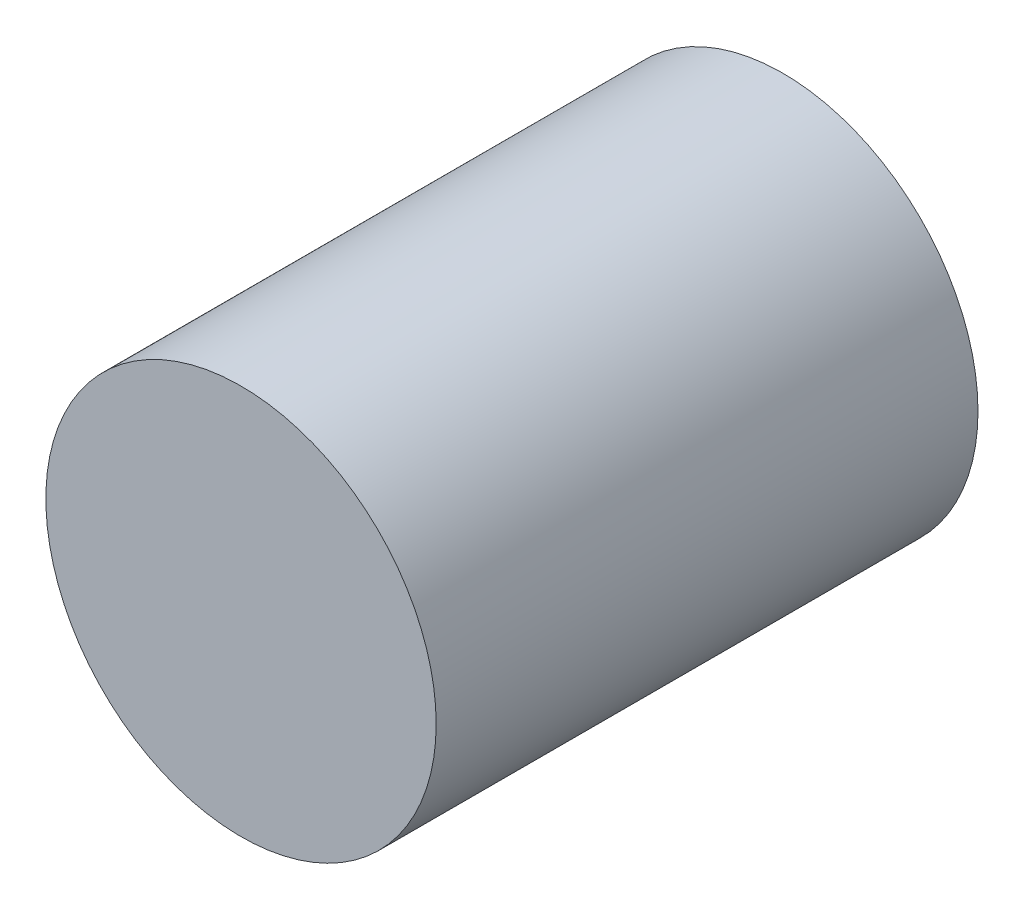
SolidWorks part; units mm, degrees
ref_plane "前视基准面" through (0, 0, 0) normal (0, 0, 1) x (1, 0, 0)
ref_plane "上视基准面" through (0, 0, 0) normal (0, 1, 0) x (1, 0, 0)
ref_plane "右视基准面" through (0, 0, 0) normal (1, 0, 0) x (0, 0, -1)
sketch "草图1" plane through (0, 0, 0) normal (0, 0, 1) x (1, 0, 0)
  circle A0 centre (0, 0) radius 19
  dimension "D1" = 38
extrude "凸台-拉伸1" add sketch "草图1" along normal blind 52.75
